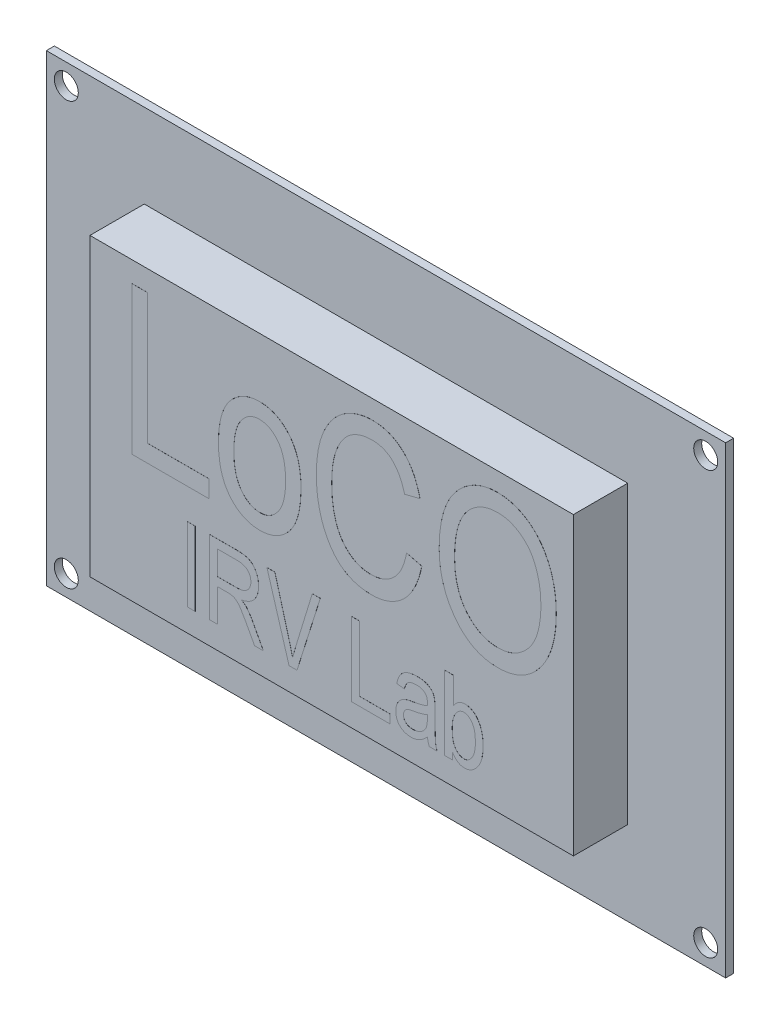
SolidWorks part; units mm, degrees
ref_plane "Front Plane" through (0, 0, 0) normal (0, 0, 1) x (1, 0, 0)
ref_plane "Top Plane" through (0, 0, 0) normal (0, 1, 0) x (1, 0, 0)
ref_plane "Right Plane" through (0, 0, 0) normal (1, 0, 0) x (0, 0, -1)
sketch "Sketch2" plane through (0, 0, 0) normal (0, 0, 1) x (1, 0, 0)
  line L1 (-42.5, -29) -> (42.5, -29)
  line L2 (-42.5, -29) -> (-42.5, 29)
  line L3 (-42.5, 29) -> (42.5, 29)
  line L4 (42.5, -29) -> (42.5, 29)
  line L5 (-42.5, -29) -> (42.5, 29) construction
  line L6 (-42.5, 29) -> (42.5, -29) construction
  circle A0 centre (-40.005, 26.415) radius 1.5
  circle A1 centre (-40.005, -26.417) radius 1.5
  circle A2 centre (40.005, -26.417) radius 1.5
  circle A3 centre (40.005, 26.415) radius 1.5
  point P0 (0, 0)
  dimension "D3" = 3
  dimension "D4" = 3
  dimension "D5" = 3
  dimension "D6" = 3
  dimension "D1" = 58
  dimension "D2" = 85
  dimension "D7" = 80.01
  dimension "D8" = 52.832
  dimension "D9" = 2.585
  dimension "D10" = 2.495
extrude "Boss-Extrude1" add sketch "Sketch2" along normal blind 1
sketch "Sketch3" plane through (0, 0, 1) normal (0, 0, 1) x (1, 0, 0)
  line L1 (-30.25, -18.5) -> (30.25, -18.5)
  line L2 (-30.25, -18.5) -> (-30.25, 18.5)
  line L3 (-30.25, 18.5) -> (30.25, 18.5)
  line L4 (30.25, -18.5) -> (30.25, 18.5)
  line L5 (-30.25, -18.5) -> (30.25, 18.5) construction
  line L6 (-30.25, 18.5) -> (30.25, -18.5) construction
  point P0 (0, 0)
  dimension "D1" = 37
  dimension "D2" = 60.5
extrude "Boss-Extrude2" add sketch "Sketch3" along normal blind 6.8
sketch "Sketch5" plane through (0, 0, 1) normal (0, 0, 1) x (1, 0, 0)
  circle A0 centre (-40.005, 26.415) radius 2.5
  circle A1 centre (-40.005, -26.417) radius 2.5
  circle A2 centre (40.005, -26.417) radius 2.5
  circle A3 centre (40.005, 26.415) radius 2.5
  dimension "D1" = 5
extrude "SHCS Test" [suppressed] add sketch "Sketch5" along normal blind 3
sketch "Sketch6" plane through (0, 0, 7.8) normal (0, 0, 1) x (1, 0, 0)
  text T0 "LoCO" font "Arial Narrow" height in points 72
extrude "Boss-Extrude3" add sketch "Sketch6" along normal blind 0.01
sketch "Sketch7" plane through (0, 0, 7.8) normal (0, 0, 1) x (1, 0, 0)
  text T0 "IRV Lab" font "Arial Narrow" height in points 36
extrude "Boss-Extrude4" add sketch "Sketch7" along normal blind 0.01
equation "\"D9@Sketch2\"=(58-52.83)/2"
equation "\"D10@Sketch2\"=(85-80.01)/2"
